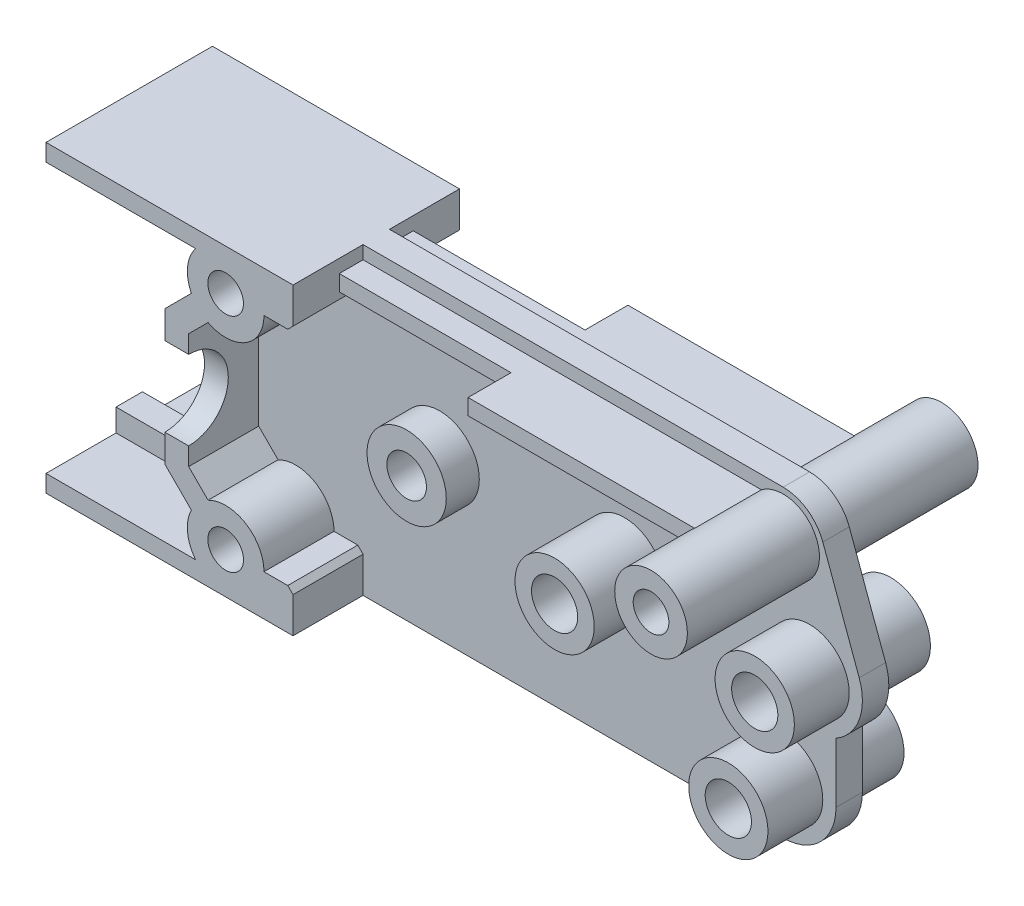
SolidWorks part; units mm, degrees
ref_plane "Front Plane" through (0, 0, 0) normal (0, 0, 1) x (1, 0, 0)
ref_plane "Top Plane" through (0, 0, 0) normal (0, 1, 0) x (1, 0, 0)
ref_plane "Right Plane" through (0, 0, 0) normal (1, 0, 0) x (0, 0, -1)
sketch "Sketch2" plane through (0, 0, 0) normal (0, 0, 1) x (1, 0, 0)
  line L0 (0, 0) -> (50.5, 0)
  line L1 (54.5, 4) -> (54.5, 8.5359)
  line L2 (53.5054, 20.8988) -> (56.2568, 13.3735)
  line L3 (50.5, 23) -> (0, 23)
  line L4 (0, 23) -> (0, 20)
  line L5 (0, 20) -> (9, 20)
  line L6 (9, 20) -> (9, 3)
  line L7 (9, 3) -> (0, 3)
  line L8 (0, 3) -> (0, 0)
  line L9 (-0.5822, 12) -> (129.0772, 12) construction
  arc A0 (54.5, 8.5359) -> (56.2568, 13.3735) centre (52.5, 12) ccw
  circle A1 centre (13.6, 3.1) radius 1.35
  circle A2 centre (24.5, 12) radius 1.5
  circle A3 centre (38.5, 12) radius 1.75
  circle A4 centre (52.5, 12) radius 1.75
  circle A5 centre (50.5, 4) radius 1.75
  arc A6 (50.5, 0) -> (54.5, 4) centre (50.5, 4) ccw
  circle A7 centre (50.5, 19.8) radius 1.35
  circle A8 centre (13.6, 19.9) radius 1.35
  arc A9 (50.5, 23) -> (53.5054, 20.8988) centre (50.5, 19.8) cw
  dimension "D3" = 2.7
  dimension "D11" = 3.5
  dimension "D12" = 3.5
  dimension "D13" = 3
  dimension "D14" = 3.5
  dimension "D16" = 7.8
  dimension "D17" = 2.7
  dimension "D18" = 4
  dimension "D19" = 3.2
  dimension "D1" = 9
  dimension "D2" = 3
  dimension "D4" = 3.1
  dimension "D5" = 13.6
  dimension "D6" = 23
  dimension "D7" = 10.9
  dimension "D8" = 14
  dimension "D9" = 12
  dimension "D10" = 2
  dimension "D15" = 8
  dimension "D20" = 12
  dimension "D21" = 3.1
extrude "Boss-Extrude1" add sketch "Sketch2" along normal mid plane 2
sketch "Sketch3" plane through (0, 0, 0) normal (0, 0, 1) x (1, 0, 0)
  circle A2 centre (52.5, 12) radius 1.75 construction
  circle A3 centre (50.5, 4) radius 1.75 construction
  circle A4 centre (50.5, 4) radius 1.75
  circle A5 centre (52.5, 12) radius 1.75
  circle A6 centre (50.5, 4) radius 3
  circle A8 centre (52.5, 12) radius 3
  dimension "D3" = 6
extrude "Boss-Extrude2" add sketch "Sketch3" along normal mid plane 10.3
sketch "Sketch4" plane through (0, 0, 0) normal (0, 0, 1) x (1, 0, 0)
  circle A0 centre (38.5, 12) radius 1.75 construction
  circle A1 centre (38.5, 12) radius 1.75
  circle A2 centre (38.5, 12) radius 3
  dimension "D1" = 6
extrude "Boss-Extrude3" add sketch "Sketch4" along normal mid plane 12.6
sketch "Sketch5" plane through (0, 0, 0) normal (0, 0, 1) x (1, 0, 0)
  circle A0 centre (24.5, 12) radius 3
  circle A1 centre (24.5, 12) radius 1.5 construction
  circle A2 centre (24.5, 12) radius 1.5
  dimension "D1" = 6
extrude "Boss-Extrude4" add sketch "Sketch5" along normal mid plane 7
sketch "Sketch6" plane through (0, 0, 0) normal (0, 0, 1) x (1, 0, 0)
  circle A0 centre (50.5, 19.8) radius 2.75
  circle A1 centre (50.5, 19.8) radius 1.35 construction
  circle A2 centre (50.5, 19.8) radius 1.35
  dimension "D1" = 5.5
extrude "Boss-Extrude5" add sketch "Sketch6" along normal mid plane 22
sketch "Sketch7" plane through (0, 0, 0) normal (0, 0, 1) x (1, 0, 0)
  line L0 (0, 23) -> (18.7, 23)
  line L1 (50.5, 23) -> (0, 23) construction
  line L2 (18.7, 23) -> (18.7, 19.9)
  line L3 (18.7, 19.9) -> (16.5, 19.9)
  line L4 (12.269, 17.3235) -> (10.8, 15.8544)
  line L5 (10.8, 15.8544) -> (10.8, 11.5)
  line L7 (9, 20) -> (9, 3) construction
  line L8 (9, 11.5) -> (9, 16.6)
  line L9 (9, 16.6) -> (11.0051, 18.6051)
  line L10 (11.3262, 21.7) -> (0, 21.7)
  line L11 (0, 23) -> (0, 20) construction
  line L12 (0, 21.7) -> (0, 23)
  line L13 (-4.917, 11.5) -> (17.4801, 11.5) construction
  line L15 (0, 1.3) -> (0, 0)
  line L16 (11.3262, 1.3) -> (0, 1.3)
  line L17 (9, 6.4) -> (11.0051, 4.3949)
  line L18 (9, 11.5) -> (9, 6.4)
  line L19 (10.8, 7.1456) -> (10.8, 11.5)
  line L20 (12.269, 5.6765) -> (10.8, 7.1456)
  line L21 (18.7, 3.1) -> (16.5, 3.1)
  line L22 (18.7, 0) -> (18.7, 3.1)
  line L23 (0, 0) -> (18.7, 0)
  arc A0 (16.5, 19.9) -> (12.269, 17.3235) centre (13.6, 19.9) cw
  arc A1 (11.0051, 18.6051) -> (11.3262, 21.7) centre (13.6, 19.9) cw
  circle A2 centre (13.6, 19.9) radius 1.35 construction
  arc A3 (11.0051, 4.3949) -> (11.3262, 1.3) centre (13.6, 3.1) ccw
  arc A4 (16.5, 3.1) -> (12.269, 5.6765) centre (13.6, 3.1) ccw
  circle A5 centre (13.6, 3.1) radius 1.35
  circle A6 centre (13.6, 19.9) radius 1.35
  circle A7 centre (13.6, 3.1) radius 1.35 construction
  dimension "D1" = 2.9
  dimension "D2" = 1.3
  dimension "D3" = 1.8
  dimension "D4" = 18.7
  dimension "D5" = 1.8
  dimension "D6" = 10.2
  dimension "D7" = 45
extrude "Boss-Extrude6" add sketch "Sketch7" along normal mid plane 12.6
ref_plane "Plane1" through (0, 22, 0) normal (0, 1, 0) x (-1, 0, 0)
sketch "Sketch8" plane through (0, 22, 0) normal (0, 1, 0) x (-1, 0, 0)
  line L0 (0, 0) -> (-67.9762, 0) construction
  line L1 (0, 6.3) -> (0, -6.3) construction
  line L2 (-18.7, -2.8) -> (-18.7, 2.8)
  line L3 (-18.7, 6.3) -> (-18.7, 1) construction
  line L4 (-18.7, 2.8) -> (-31.7, 2.8)
  line L5 (-31.7, 2.8) -> (-31.7, 6.05)
  line L6 (-31.7, 6.05) -> (-50.5, 6.05)
  line L7 (-50.5, 6.05) -> (-50.5, -6.05)
  line L8 (-50.5, 1) -> (-50.5, -1) construction
  line L9 (-31.7, -6.05) -> (-50.5, -6.05)
  line L10 (-31.7, -2.8) -> (-31.7, -6.05)
  line L11 (-18.7, -2.8) -> (-31.7, -2.8)
  point P15 (-50.5, 0)
  point P18 (-18.7, 0)
  dimension "D1" = 13
  dimension "D2" = 12.1
  dimension "D3" = 5.6
extrude "Boss-Extrude7" add sketch "Sketch8" against normal blind 1.2
sketch "Sketch9" plane through (0, 0, -11) normal (0, 0, -1) x (-1, 0, 0)
  circle A0 centre (-50.5, 19.8) radius 1.35 construction
  circle A3 centre (-50.5, 19.8) radius 1.35
extrude "Cut-Extrude1" cut sketch "Sketch9" against normal through all
sketch "Sketch10" plane through (9, 0, 0) normal (-1, 0, 0) x (0, 0, 1)
  line L0 (6.3, 16.6) -> (6.3, 6.4) construction
  line L1 (0, 23) -> (0, 0) construction
  line L2 (6.3, 23) -> (-6.3, 23) construction
  line L3 (6.3, 0) -> (-6.3, 0) construction
  line L4 (-6.3, 14.5) -> (-6.3, 8.5)
  line L5 (6.3, 8.5) -> (6.3, 14.5)
  line L6 (6.3, 14.5) -> (6.305, 14.5649)
  arc A0 (6.3, 8.5) -> (6.3, 14.5) centre (6.3, 11.5) cw
  arc A1 (-6.3, 8.5) -> (-6.3, 14.5) centre (-6.3, 11.5) ccw
  dimension "D1" = 3
extrude "Cut-Extrude2" cut sketch "Sketch10" against normal up to next contours A1 L4 | L5 A0
chamfer "Chamfer2" distance 0.4 angle 45 4 edges at (18.7, 19.9, -3.65) (18.7, 3.1, -3.65) (18.7, 3.1, 3.65) (18.7, 19.9, 3.65)
